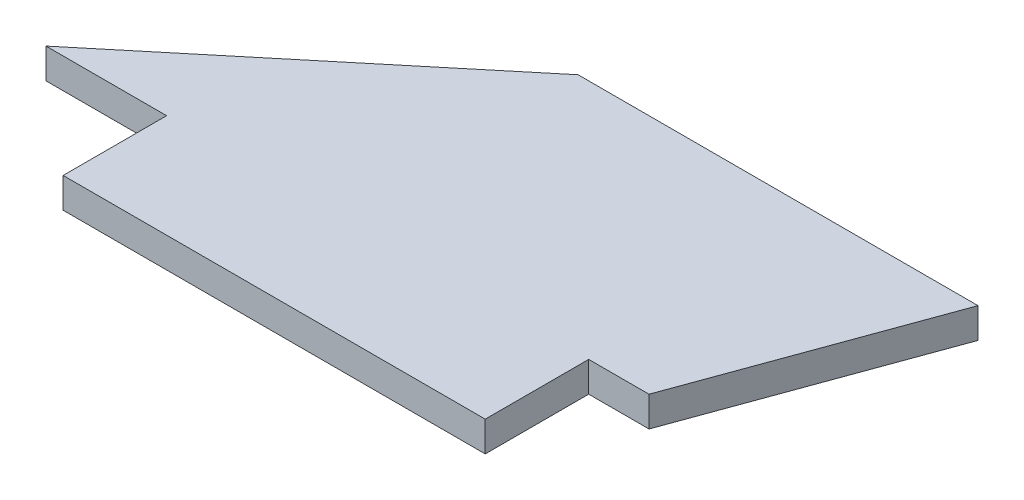
SolidWorks part; units mm, degrees
ref_plane "Front Plane" through (0, 0, 0) normal (0, 0, 1) x (1, 0, 0)
ref_plane "Top Plane" through (0, 0, 0) normal (0, 1, 0) x (1, 0, 0)
ref_plane "Right Plane" through (0, 0, 0) normal (1, 0, 0) x (0, 0, -1)
sketch "Sketch1" plane through (0, 0, 0) normal (0, 1, 0) x (1, 0, 0)
  line L0 (0, 0) -> (20, 0)
  line L1 (20, 0) -> (20, -17.16)
  line L2 (20, -17.16) -> (90, -17.16)
  line L3 (90, -17.16) -> (90, 0)
  line L4 (90, 0) -> (100, 0)
  line L5 (100, 0) -> (114.5588, 40)
  line L6 (114.5588, 40) -> (48.2388, 40)
  line L7 (48.2388, 40) -> (0, 0)
  dimension "D1" = 20
  dimension "D2" = 70
  dimension "D3" = 17.16
  dimension "D4" = 100
  dimension "D5" = 66.32
  dimension "D6" = 40
  dimension "D7" = 70
extrude "Boss-Extrude1" add sketch "Sketch1" along normal mid plane 5
